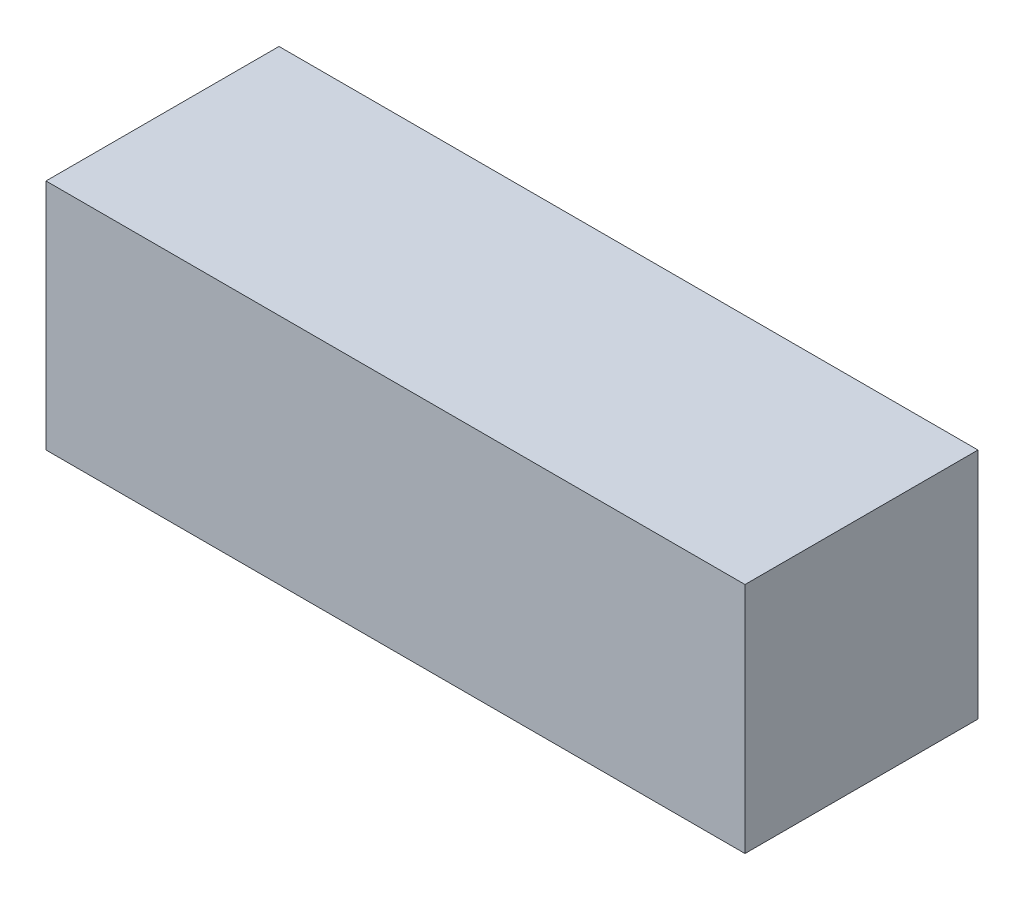
SolidWorks part; units mm, degrees
ref_plane "Спереди" through (0, 0, 0) normal (0, 0, 1) x (1, 0, 0)
ref_plane "Сверху" through (0, 0, 0) normal (0, 1, 0) x (1, 0, 0)
ref_plane "Справа" through (0, 0, 0) normal (1, 0, 0) x (0, 0, -1)
sketch "Эскиз1" plane through (0, 0, 0) normal (0, 1, 0) x (1, 0, 0)
  line L1 (-3, 1) -> (3, 1)
  line L2 (-3, 1) -> (-3, -1)
  line L3 (-3, -1) -> (3, -1)
  line L4 (3, 1) -> (3, -1)
  line L5 (0, -1) -> (0, 1) construction
  line L6 (-3, 0) -> (3, 0) construction
  point P0 (0, 0)
  dimension "D1" = 6
  dimension "D2" = 2
extrude "Бобышка-Вытянуть1" add sketch "Эскиз1" along normal blind 2
